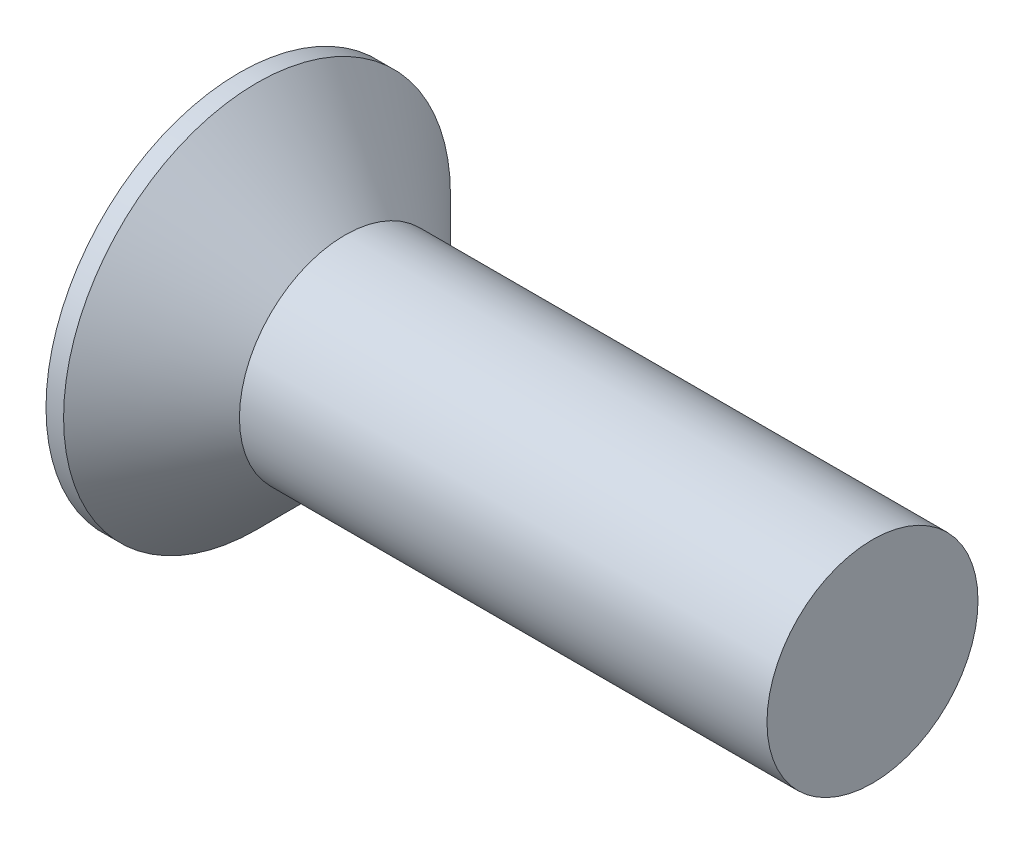
SolidWorks part; units mm, degrees
material "AISI 1020"
ref_plane "Спереди" through (0, 0, 0) normal (0, 0, 1) x (1, 0, 0)
ref_plane "Сверху" through (0, 0, 0) normal (0, 1, 0) x (1, 0, 0)
ref_plane "Справа" through (0, 0, 0) normal (1, 0, 0) x (0, 0, -1)
sketch "Эскиз1" plane through (0, 0, 0) normal (0, 0, 1) x (1, 0, 0)
  line L0 (-1000, 0) -> (49000, 0) construction
  line L1 (-3, 0) -> (-3, 5.5)
  line L2 (-3, 5.5) -> (-2.5, 5.5)
  line L3 (-2.5, 5.5) -> (0, 3)
  line L4 (0, 3) -> (15, 3)
  line L5 (15, 3) -> (15, 0)
  line L6 (-3, 0) -> (15, 0)
  dimension "D1" = 45
  dimension "D2" = 3
  dimension "D3" = 6
  dimension "D4" = 11
  dimension "D5" = 15
revolve "Повернуть1" add sketch "Эскиз1" angle 360 about L0
cosmetic thread "Условное изображение резьбы1" parameters "D2"=4.891
